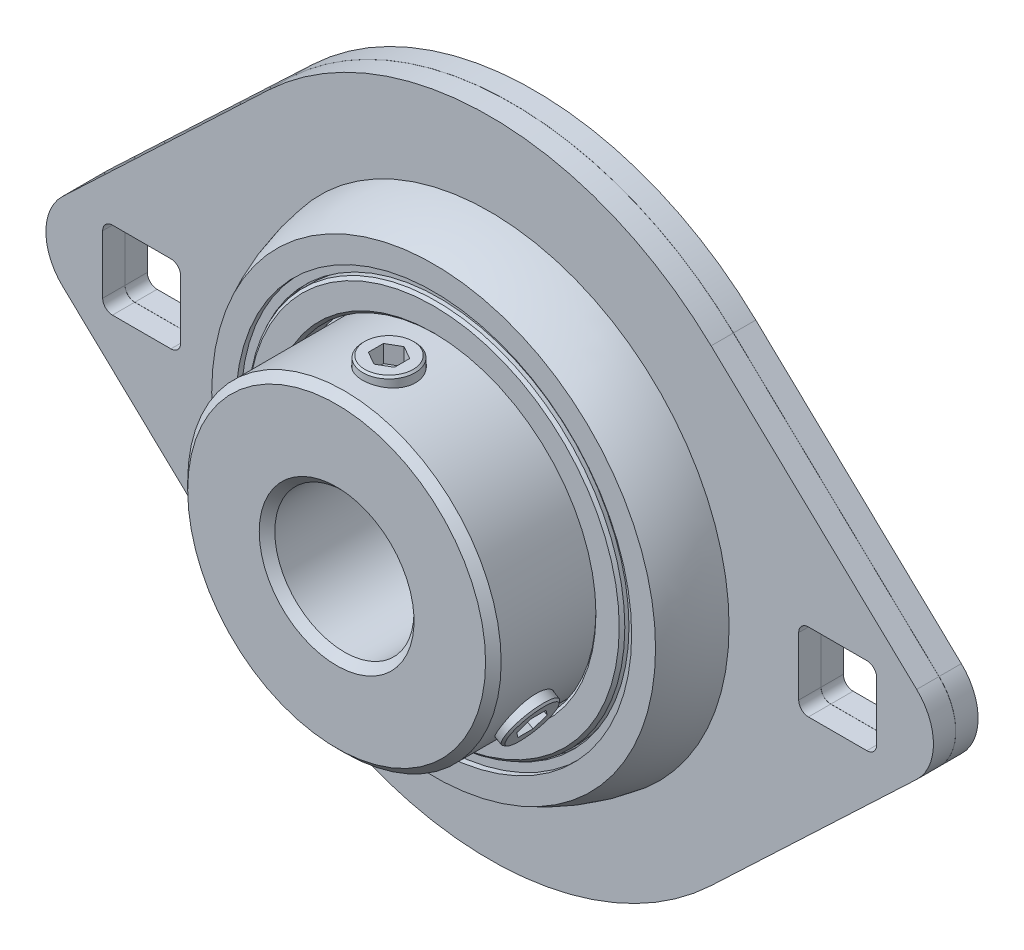
SolidWorks part; units mm, degrees
ref_plane "Front" through (0, 0, 0) normal (0, 0, 1) x (1, 0, 0)
ref_plane "Top" through (0, 0, 0) normal (0, 1, 0) x (1, 0, 0)
ref_plane "Right" through (0, 0, 0) normal (1, 0, 0) x (0, 0, -1)
sketch "Sketch1" plane through (0, 0, 0) normal (1, 0, 0) x (0, 0, -1)
  line L0 (-15.9995, 6.35) -> (5.9995, 6.35)
  line L1 (5.9995, 6.35) -> (5.9995, 14.3002)
  line L2 (5.9995, 14.3002) -> (2.6769, 14.3002)
  line L3 (-15.9995, 14.3002) -> (-15.9995, 6.35)
  line L4 (-4.8006, 19.3408) -> (4.8006, 19.3408) construction
  line L5 (4.8006, 19.3408) -> (4.8006, 18.7309) construction
  line L6 (-4.8006, 18.7269) -> (-4.8006, 19.3408) construction
  line L7 (0.0051, 29.3751) -> (0.0051, 19.9447)
  line L8 (5.1181, 18.9465) -> (5.1181, 14.5542)
  line L10 (7.1501, 14.5542) -> (7.1501, 17.1896)
  line L11 (2.0371, 21.844) -> (2.0371, 29.3751)
  line L12 (2.0371, 29.3751) -> (0.0051, 29.3751)
  line L13 (0.0051, 6.35) -> (1.7729, 19.8293) construction
  line L14 (1.7729, 19.8293) -> (2.0371, 21.844) construction
  line L15 (0, 16.8205) -> (0, 29.3751) construction
  line L16 (0, 29.3751) -> (0.0051, 29.3751) construction
  line L17 (-2.0371, 29.3751) -> (-0.0051, 29.3751)
  line L18 (-2.0371, 21.844) -> (-2.0371, 29.3751)
  line L19 (-7.1501, 14.5542) -> (-7.1501, 17.1896)
  line L21 (-5.1181, 18.9465) -> (-5.1181, 14.5542)
  line L22 (-0.0051, 29.3751) -> (-0.0051, 19.9447)
  line L23 (-5.1181, 0) -> (5.1181, 0) construction
  line L24 (0, 0) -> (0, 6.35) construction
  line L25 (0.0051, 19.9447) -> (0.0051, 19.6272) construction
  line L26 (4.8006, 18.7309) -> (5.1181, 18.7309) construction
  line L27 (0, 19.3408) -> (0, 20.421) construction
  line L28 (0, 14.3002) -> (0, 13.2201) construction
  line L29 (0, 20.421) -> (0, 20.4972) construction
  line L30 (-7.1501, 14.5542) -> (-5.1181, 14.5542)
  line L31 (-2.6769, 14.3002) -> (-15.9995, 14.3002)
  line L32 (5.1181, 14.5542) -> (7.1501, 14.5542)
  line L33 (2.6769, 14.3002) -> (-2.6769, 14.3002) construction
  line L34 (-7.1501, 17.1896) -> (-6.1341, 17.1896)
  line L35 (-6.1341, 17.1896) -> (-6.1341, 17.3166)
  line L36 (-6.1341, 17.3166) -> (-6.6421, 17.3166)
  line L37 (-6.6421, 17.3166) -> (-6.6421, 18.0681)
  line L38 (-6.6421, 18.0681) -> (-7.1501, 18.0681)
  line L39 (-7.1501, 18.0681) -> (-7.1501, 20.2475)
  line L40 (-6.1341, 17.1896) -> (-6.1341, 14.5542) construction
  line L41 (-6.6421, 17.3166) -> (-6.6421, 17.1896) construction
  line L42 (6.6421, 18.0681) -> (7.1501, 18.0681)
  line L43 (6.6421, 17.3166) -> (6.6421, 18.0681)
  line L44 (6.1341, 17.3166) -> (6.6421, 17.3166)
  line L45 (7.1501, 17.1896) -> (6.1341, 17.1896)
  line L46 (6.1341, 17.1896) -> (6.1341, 17.3166)
  line L47 (7.1501, 18.0681) -> (7.1501, 20.2475)
  arc A0 (4.8006, 18.7309) -> (-4.8006, 18.7269) centre (0.0051, 6.35) ccw construction
  arc A1 (0.0051, 19.9447) -> (5.1181, 18.9465) centre (0.0051, 6.35) cw
  arc A2 (7.1501, 20.2475) -> (2.0371, 21.844) centre (0.0051, 6.35) ccw
  circle A3 centre (0, 16.8205) radius 3.6005 construction
  arc A4 (-7.1501, 20.2475) -> (-2.0371, 21.844) centre (-0.0051, 6.35) cw
  arc A5 (-0.0051, 19.9447) -> (-5.1181, 18.9465) centre (-0.0051, 6.35) ccw
  arc A6 (-2.6769, 19.3408) -> (2.6769, 19.3408) centre (0, 16.8205) cw construction
  arc A7 (-2.6769, 14.3002) -> (2.6769, 14.3002) centre (0, 16.8205) ccw
  dimension "D4" = 7.2009
  dimension "D1" = 0.0051
  dimension "Material Thickness t" = 2.032
  dimension "D2" = 0.3175
  dimension "Shaft Dia" = 12.7
  dimension "Bearing OD K" = 28.6004
  dimension "Bearing Length Bi" = 21.9989
  dimension "Bearing Back n" = 5.9995
  dimension "Bearing Thickness M" = 7.145
  dimension "OD b" = 58.7502
  dimension "D3" = 9.6012
  dimension "D5" = 1.0801
  dimension "D6" = 0.0762
  dimension "D7" = 0.254
  dimension "D9" = 0.127
  dimension "D10" = 4.3923
  dimension "D11" = 2.6354
  dimension "D12" = 0.8785
  dimension "Bearing Dia" = 43.688
revolve "Revolve1" add sketch "Sketch1" angle 360 about L23
chamfer "Chamfer3" distance 0.254 angle 45 2 edges at (17.1896, 0, 7.1501) (14.5542, 0, 7.1501)
chamfer "Chamfer4" distance 0.254 angle 45 2 edges at (14.5542, 0, -7.1501) (17.1896, 0, -7.1501)
sketch "Sketch3" plane through (0, 0, 0) normal (1, 0, 0) x (0, 0, -1)
  line L0 (0, 14.3002) -> (0, 13.2201) construction
  line L1 (0, 20.421) -> (0, 13.2201)
  circle A0 centre (0, 16.8205) radius 3.6005 construction
  arc A1 (0, 13.2201) -> (0, 20.421) centre (0, 16.8205) ccw
revolve "Revolve3" add sketch "Sketch3" angle 360 about L1
pattern_circular "CirPattern1" count 4 over 360 about axis through (0, 0, 0) along (0, 0, 1) of bodies 113
sketch "Sketch4" plane through (0, 0, 2.0371) normal (0, 0, 1) x (1, 0, 0)
  line L0 (-20.2029, 21.3246) -> (-38.9581, 3.556)
  line L1 (-38.9581, -3.556) -> (-20.2029, -21.3246)
  line L2 (-35.5891, 0) -> (35.5891, 0) construction
  line L3 (-31.75, -3.556) -> (-31.75, 3.556) construction
  line L4 (20.2029, -21.3246) -> (38.9581, -3.556)
  line L5 (38.9581, 3.556) -> (20.2029, 21.3246)
  line L6 (-35.306, -3.556) -> (-28.194, -3.556) construction
  line L7 (-35.306, -3.556) -> (-35.306, 3.556) construction
  line L8 (-35.306, 3.556) -> (-28.194, 3.556) construction
  line L9 (-28.194, -3.556) -> (-28.194, 3.556) construction
  line L10 (-20.2029, 21.3246) -> (20.2029, 21.3246) construction
  line L11 (0, 0) -> (0, 21.3246) construction
  line L12 (35.306, -3.556) -> (28.194, -3.556) construction
  line L13 (35.306, -3.556) -> (35.306, 3.556) construction
  line L14 (35.306, 3.556) -> (28.194, 3.556) construction
  line L15 (28.194, -3.556) -> (28.194, 3.556) construction
  line L16 (31.75, 3.556) -> (31.75, -3.556) construction
  arc A0 (-20.2029, 21.3246) -> (-20.2029, -21.3246) centre (0, 0) ccw
  arc A1 (-38.9581, 3.556) -> (-38.9581, -3.556) centre (-35.5891, 0) ccw
  arc A2 (38.9581, -3.556) -> (38.9581, 3.556) centre (35.5891, 0) ccw
  arc A3 (20.2029, -21.3246) -> (20.2029, 21.3246) centre (0, 0) ccw
  dimension "Overall Length a" = 80.9752
  dimension "Square length s" = 7.112
  dimension "Hole Distance e" = 63.5
extrude "Extrude1" add sketch "Sketch4" against normal up to surface (2.032 mm away) up to face at (29.3751, 0, 0.0051)
sketch "Sketch5" plane through (0, 0, -2.0371) normal (0, 0, -1) x (-1, 0, 0)
  line L0 (20.2029, 21.3246) -> (38.9581, 3.556) construction
  line L1 (38.9581, -3.556) -> (20.2029, -21.3246) construction
  line L2 (-20.2029, -21.3246) -> (-38.9581, -3.556) construction
  line L3 (-38.9581, 3.556) -> (-20.2029, 21.3246) construction
  line L4 (20.2029, 21.3246) -> (38.9581, 3.556)
  line L5 (38.9581, -3.556) -> (20.2029, -21.3246)
  line L6 (-20.2029, -21.3246) -> (-38.9581, -3.556)
  line L7 (-38.9581, 3.556) -> (-20.2029, 21.3246)
  arc A0 (38.9581, -3.556) -> (38.9581, 3.556) centre (35.5891, 0) ccw construction
  arc A1 (20.2029, -21.3246) -> (20.2029, 21.3246) centre (0, 0) ccw construction
  arc A2 (-38.9581, 3.556) -> (-38.9581, -3.556) centre (-35.5891, 0) ccw construction
  arc A3 (-20.2029, 21.3246) -> (-20.2029, -21.3246) centre (0, 0) ccw construction
  arc A4 (38.9581, -3.556) -> (38.9581, 3.556) centre (35.5891, 0) ccw
  arc A5 (20.2029, -21.3246) -> (20.2029, 21.3246) centre (0, 0) ccw
  arc A6 (-38.9581, 3.556) -> (-38.9581, -3.556) centre (-35.5891, 0) ccw
  arc A7 (-20.2029, 21.3246) -> (-20.2029, -21.3246) centre (0, 0) ccw
extrude "Extrude2" add sketch "Sketch5" against normal up to surface (2.032 mm away) up to face at (19.9447, 0, -0.0051)
sketch "Sketch6" plane through (0, 0, 0) normal (0, 0, 1) x (1, 0, 0)
  line L0 (35.306, -3.556) -> (28.194, -3.556) construction
  line L1 (35.306, -3.556) -> (35.306, 3.556) construction
  line L2 (35.306, 3.556) -> (28.194, 3.556) construction
  line L3 (28.194, -3.556) -> (28.194, 3.556) construction
  line L4 (-28.194, -3.556) -> (-28.194, 3.556) construction
  line L5 (-35.306, -3.556) -> (-28.194, -3.556) construction
  line L6 (-35.306, -3.556) -> (-35.306, 3.556) construction
  line L7 (-35.306, 3.556) -> (-28.194, 3.556) construction
  line L8 (35.306, -3.556) -> (28.194, -3.556)
  line L9 (35.306, -3.556) -> (35.306, 3.556)
  line L10 (35.306, 3.556) -> (28.194, 3.556)
  line L11 (28.194, -3.556) -> (28.194, 3.556)
  line L12 (-28.194, -3.556) -> (-28.194, 3.556)
  line L13 (-35.306, -3.556) -> (-28.194, -3.556)
  line L14 (-35.306, -3.556) -> (-35.306, 3.556)
  line L15 (-35.306, 3.556) -> (-28.194, 3.556)
extrude "Cut-Extrude1" cut sketch "Sketch6" against normal through all and the other way through all
fillet "Fillet1" radius 0.889 8 edges at (35.306, -3.556, -1.0211) (35.306, 3.556, -1.0211) (28.194, 3.556, -1.0211) (28.194, -3.556, -1.0211) (-35.306, -3.556, -1.0211) (-28.194, -3.556, -1.0211) (-28.194, 3.556, -1.0211) (-35.306, 3.556, -1.0211)
fillet "Fillet2" radius 0.889 8 edges at (35.306, -3.556, 1.0211) (28.194, -3.556, 1.0211) (28.194, 3.556, 1.0211) (35.306, 3.556, 1.0211) (-28.194, -3.556, 1.0211) (-28.194, 3.556, 1.0211) (-35.306, 3.556, 1.0211) (-35.306, -3.556, 1.0211)
chamfer "Chamfer1" distance 0.7112 angle 45 3 edges at (6.35, 0, -5.9995) (6.35, 0, 15.9995) (14.3002, 0, 15.9995)
sketch "Sketch7" plane through (0, 0, 0) normal (1, 0, 0) x (0, 0, -1)
  line L0 (-11.2192, 14.3002) -> (-11.2192, 6.35) construction
  line L1 (-2.6769, 14.3002) -> (-15.9995, 14.3002) construction
  line L2 (-15.9995, 6.35) -> (5.9995, 6.35) construction
  line L3 (-7.1501, 15.0622) -> (-7.1501, 14.3002) construction
  line L4 (-7.1501, 20.2475) -> (-7.1501, -20.2475) construction
  line L5 (-2.6769, 14.3002) -> (-15.2883, 14.3002) construction
  line L6 (-11.2192, 14.3002) -> (-13.6322, 14.3002) construction
  line L7 (-11.2192, 15.0622) -> (-15.2883, 15.0622) construction
  line L8 (-11.2192, 15.0622) -> (-7.1501, 15.0622) construction
  line L9 (-13.6322, 0) -> (-11.2192, 0)
  line L10 (-13.6322, 0) -> (-13.6322, 15.0622)
  line L11 (-13.6322, 15.0622) -> (-11.2192, 15.0622)
  line L12 (-11.2192, 0) -> (-11.2192, 15.0622)
  line L13 (0, 0) -> (-11.2192, 0) construction
  line L14 (-15.2883, 14.3002) -> (-15.2883, -14.3002) construction
  line L15 (-11.2192, 15.0622) -> (-11.2192, 16.8744) construction
  dimension "D1" = 0.762
  dimension "SD" = 4.826
revolve "Cut-Revolve2" cut sketch "Sketch7" angle 360 about L12
sketch "Sketch8" plane through (0, 0, 0) normal (1, 0, 0) x (0, 0, -1)
  line L0 (-13.6068, 15.0622) -> (-13.6068, 7.0979)
  line L1 (-13.6068, 7.0979) -> (-13.3346, 6.35)
  line L2 (-13.3346, 6.35) -> (-11.2192, 6.35)
  line L3 (-11.2192, 6.35) -> (-11.2192, 15.0622)
  line L4 (-13.6068, 15.0622) -> (-12.8109, 15.0622)
  line L6 (-11.2192, 0) -> (-11.2192, 15.0622) construction
  line L7 (-13.6322, 0) -> (-13.6322, 15.0622) construction
  line L8 (-15.9995, 6.35) -> (5.9995, 6.35) construction
  line L9 (-13.6322, 15.0622) -> (-11.2192, 15.0622) construction
  line L10 (-12.8109, 15.0622) -> (-12.015, 15.0622)
  line L11 (-12.015, 15.0622) -> (-11.2192, 15.0622)
  line L12 (-11.2192, 6.35) -> (-11.2192, -2.3622) construction
  line L14 (-8.8316, 15.0622) -> (-8.8316, 7.0979) construction
  dimension "D1" = 0.0254
  dimension "D2" = 70
  dimension "D3" = 4.7752
  dimension "D4" = 7.9643
revolve "Revolve4" add sketch "Sketch8" angle 360 about L3
chamfer "Chamfer2" distance 0.1778 angle 45 1 edges at (0, 15.0622, 8.8316)
sketch "Sketch9" plane through (0, 15.0622, 0) normal (0, 1, 0) x (-1, 0, 0)
  line L1 (0, 9.8407) -> (1.1938, 10.5299)
  line L2 (1.1938, 10.5299) -> (1.1938, 11.9084)
  line L3 (1.1938, 11.9084) -> (0, 12.5977)
  line L4 (0, 12.5977) -> (-1.1938, 11.9084)
  line L5 (-1.1938, 11.9084) -> (-1.1938, 10.5299)
  line L6 (-1.1938, 10.5299) -> (0, 9.8407)
  circle A0 centre (0, 11.2192) radius 1.1938 construction
  dimension "D1" = 2.3876
extrude "Cut-Extrude2" cut sketch "Sketch9" against normal blind 1.5929
pattern_circular "CirPattern2" count 2 every 120 of "Cut-Revolve2"
pattern_circular "CirPattern3" count 2 every 120 about axis through (0, 0, 0) along (0, 0, 1) of bodies 124
equation "\"D4@Sketch1\"=\"D3@Sketch1\"*.75"
equation "\"D5@Sketch1\"=\"D4@Sketch1\"*.15"
equation "\"D1@Fillet1\"=\"Square length s@Sketch4\"/8"
equation "\"D1@Fillet2\"=\"D1@Fillet1\""
equation "\"D1@Chamfer1\"=\"Square length s@Sketch4\"/10"
equation "\"D1@Chamfer2\"=\"Square length s@Sketch4\"/40"
equation "\"D1@Sketch9\"=\"D3@Sketch8\"/2"
equation "\"D1@Cut-Extrude2\"=\"D4@Sketch8\"/5"
equation "\"D12@Sketch1\"=\"D10@Sketch1\"*.2"
equation "\"D11@Sketch1\"=\"D10@Sketch1\"*.6"
